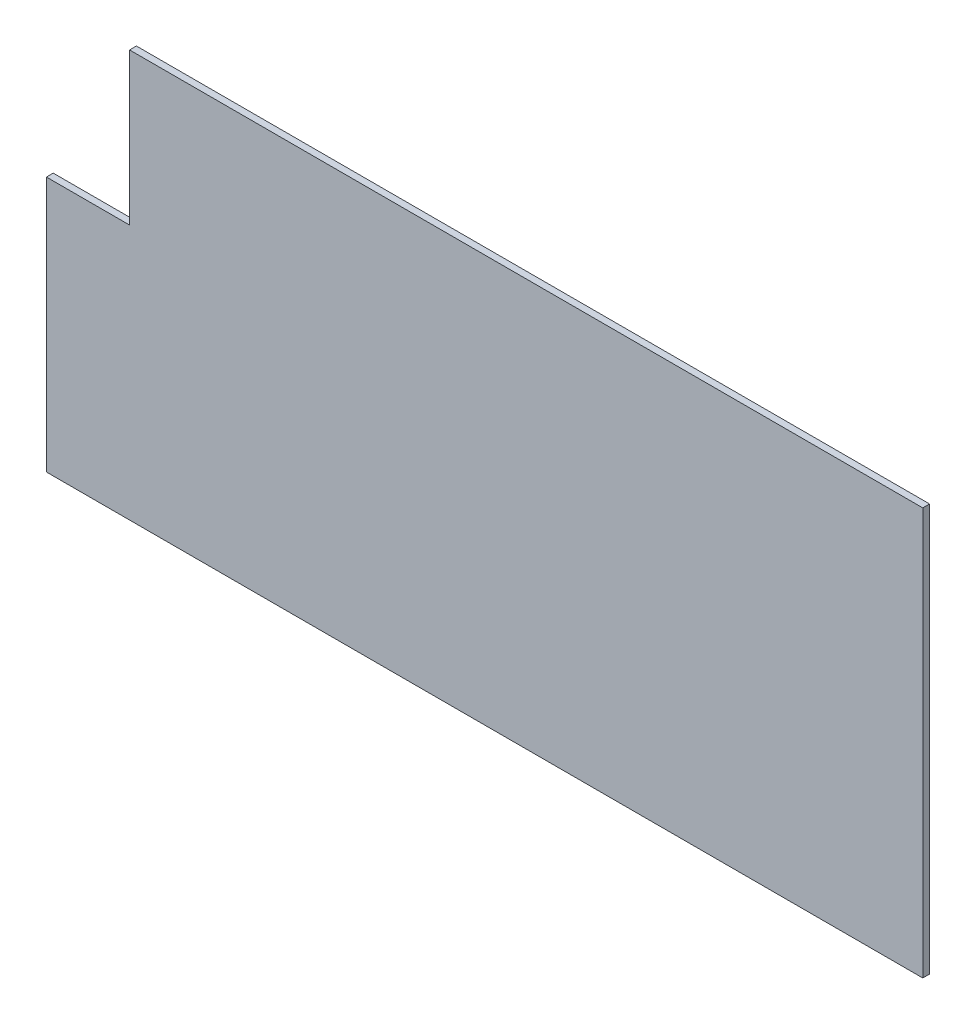
SolidWorks part; units mm, degrees
material "Acrylic (Medium-high impact)"
ref_plane "Front Plane" through (0, 0, 0) normal (0, 0, 1) x (1, 0, 0)
ref_plane "Top Plane" through (0, 0, 0) normal (0, 1, 0) x (1, 0, 0)
ref_plane "Right Plane" through (0, 0, 0) normal (1, 0, 0) x (0, 0, -1)
sketch "Sketch1" plane through (0, 0, 0) normal (0, 0, 1) x (1, 0, 0)
  line L1 (-289.5, -134.5) -> (289.5, -134.5)
  line L2 (-289.5, -134.5) -> (-289.5, 134.5)
  line L3 (-289.5, 134.5) -> (289.5, 134.5)
  line L4 (289.5, -134.5) -> (289.5, 134.5)
  line L5 (-289.5, -134.5) -> (289.5, 134.5) construction
  line L6 (-289.5, 134.5) -> (289.5, -134.5) construction
  point P0 (0, 0)
  dimension "D1" = 579
  dimension "D2" = 269
extrude "Boss-Extrude1" add sketch "Sketch1" along normal mid plane 4.4958
sketch "Sketch2" plane through (0, 0, -2.2479) normal (0, 0, -1) x (-1, 0, 0)
  line L0 (236.25, 35.3) -> (284.75, 35.3) construction
  line L1 (235.55, 35.3) -> (289.5, 35.3) construction
  line L2 (235.55, 36) -> (235.55, 134) construction
  line L3 (235.55, 35.3) -> (235.55, 134.5) construction
  line L4 (289.5, 34.3) -> (289.5, 134.5)
  line L5 (289.5, 134.5) -> (289.5, -134.5) construction
  line L6 (289.5, 134.5) -> (234.55, 134.5)
  line L7 (234.55, 34.3) -> (234.55, 134.5)
  line L10 (234.55, 34.3) -> (289.5, 34.3)
  line L11 (289.5, 35.3) -> (289.5, 134.5) construction
  line L12 (289.5, 134.5) -> (235.55, 134.5) construction
  line L13 (234.55, 34.3) -> (234.55, 135.5) construction
  line L14 (234.55, 34.3) -> (290.5, 34.3) construction
  line L15 (290.5, 34.3) -> (290.5, 135.5) construction
  line L16 (290.5, 135.5) -> (234.55, 135.5) construction
  dimension "D1" = 1
extrude "Cut-Extrude1" cut sketch "Sketch2" against normal up to surface (4.4958 mm away) up to face at (0, 0, 2.2479)
